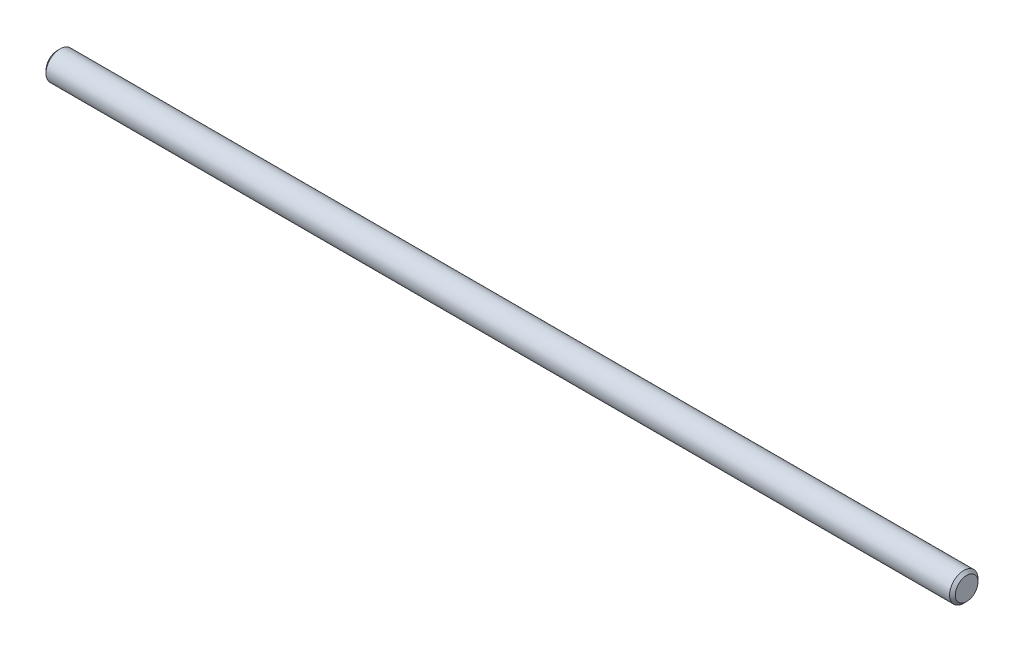
SolidWorks part; units mm, degrees
ref_plane "Front" through (0, 0, 0) normal (0, 0, 1) x (1, 0, 0)
ref_plane "Top" through (0, 0, 0) normal (0, 1, 0) x (1, 0, 0)
ref_plane "Right" through (0, 0, 0) normal (1, 0, 0) x (0, 0, -1)
sketch "Sketch1" plane through (0, 0, 0) normal (0, 0, 1) x (1, 0, 0)
  line L0 (-101.6, 0) -> (101.6, 0) construction
  line L1 (101.6, 3.175) -> (101.6, -3.175) construction
  line L2 (-101.6, 3.175) -> (-101.6, -3.175) construction
  dimension "Length" = 203.2
  dimension "Diameter" = 6.35
sketch "Sketch2" plane through (0, 0, 0) normal (1, 0, 0) x (0, 0, -1)
  circle A0 centre (0, 0) radius 3.175
extrude "Extrude1" add sketch "Sketch2" against normal up to vertex (101.6 mm away) and the other way up to vertex (101.6 mm away) up to point (-101.6, 3.175, 0) other way up to point (101.6, 3.175, 0)
chamfer "Chamfer1" distance 0.635 angle 45 2 edges at (101.6, 0, -3.175) (-101.6, 0, -3.175)
equation "\"D1@Chamfer1\" = \"Diameter@Sketch1\"*.1"
